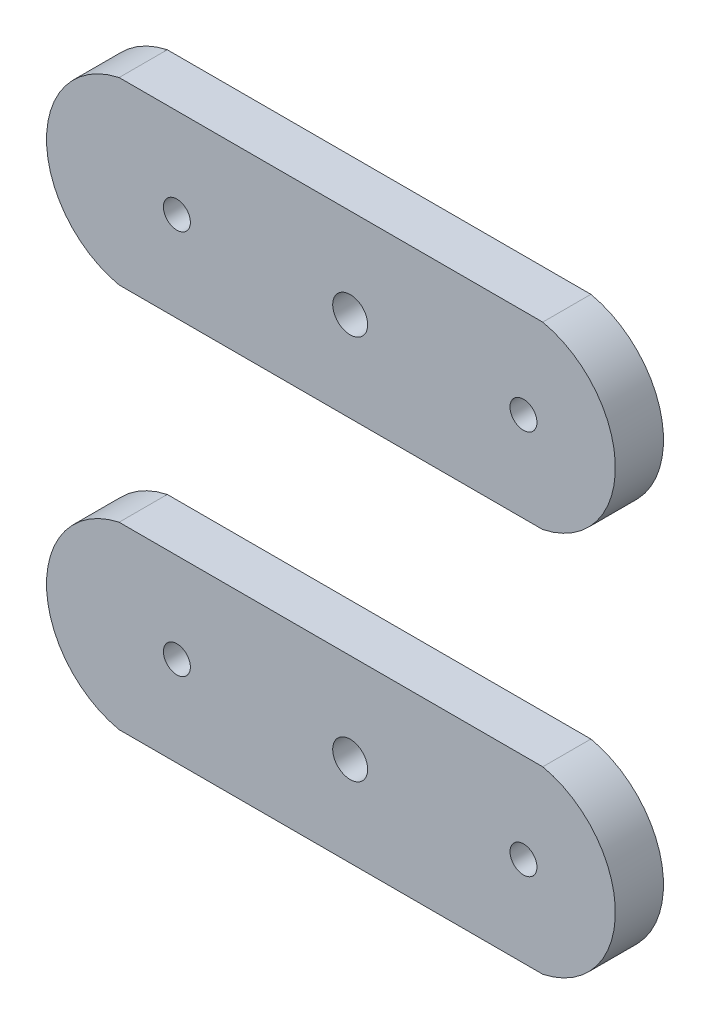
SolidWorks part; units mm, degrees
ref_plane "Front Plane" through (0, 0, 0) normal (0, 0, 1) x (1, 0, 0)
ref_plane "Top Plane" through (0, 0, 0) normal (0, 1, 0) x (1, 0, 0)
ref_plane "Right Plane" through (0, 0, 0) normal (1, 0, 0) x (0, 0, -1)
ref_plane "Plane9" through (0, 0, 0) normal (0, 0, 1) x (1, 0, 0)
sketch "Sketch9" plane through (0, 0, 0) normal (0, 0, 1) x (1, 0, 0)
  line L0 (19.05, 0) -> (69.85, 0)
  line L1 (69.85, 23.6985) -> (19.05, 23.6985)
  line L2 (44.45, 0) -> (44.45, 23.6985) construction
  line L3 (19.05, 23.6985) -> (13.97, 23.6985)
  line L4 (19.05, 0) -> (13.97, 0)
  circle A0 centre (44.45, 11.8493) radius 2.305
  circle A1 centre (67.31, 11.8493) radius 1.778
  circle A2 centre (21.59, 11.8493) radius 1.778
  arc A3 (13.97, 0) -> (13.97, 23.6985) centre (16.51, 11.8493) cw
  arc A4 (69.85, 0) -> (69.85, 23.6985) centre (67.31, 11.8493) ccw
  point P4 (44.45, 23.6985)
  point P5 (44.45, 11.8493)
  dimension "D1" = 4.61
  dimension "D5" = 3.556
  dimension "D6" = 3.556
  dimension "D7" = 5.08
  dimension "D2" = 22.86
  dimension "D3" = 50.8
  dimension "D4" = 22.86
extrude "Boss-Extrude1" add sketch "Sketch9" along normal blind 6.35
move or copy body "Body-Move/Copy1" bodies to move or copy 101 copy yes number of copies 1 translate (0, 50.8, 0)
